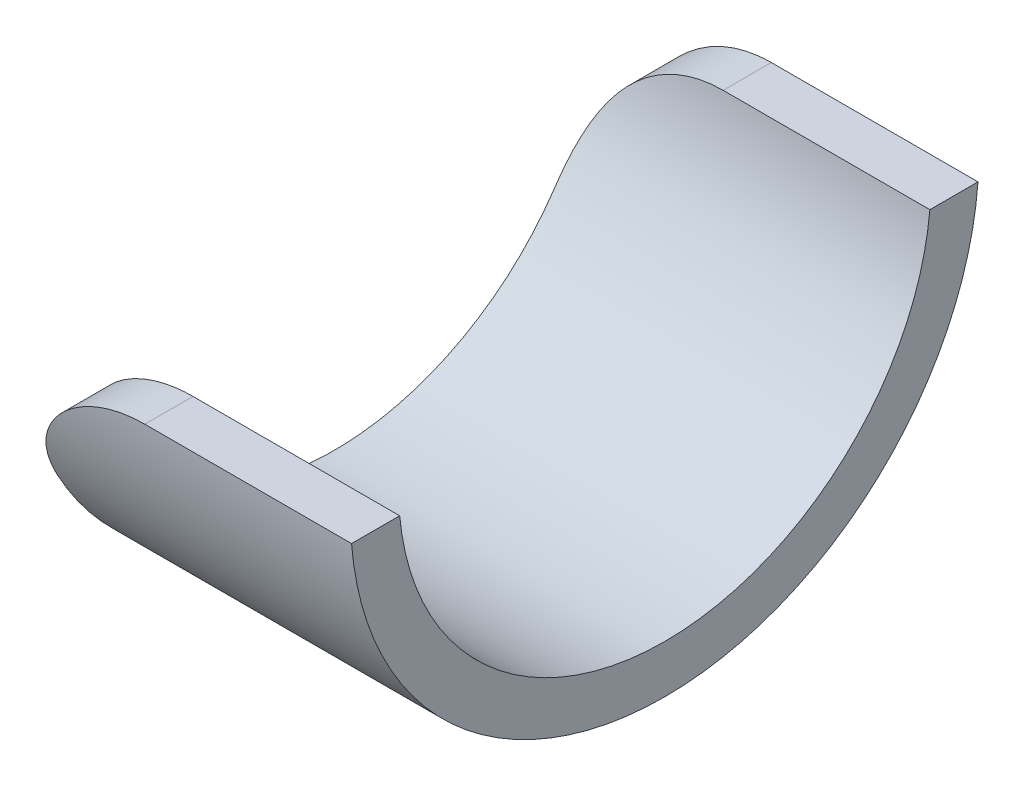
SolidWorks part; units mm, degrees
material "6061-T6 (SS)"
ref_plane "Front Plane" through (0, 0, 0) normal (0, 0, 1) x (1, 0, 0)
ref_plane "Top Plane" through (0, 0, 0) normal (0, 1, 0) x (1, 0, 0)
ref_plane "Right Plane" through (0, 0, 0) normal (1, 0, 0) x (0, 0, -1)
sketch "Sketch1" plane through (0, 0, 0) normal (1, 0, 0) x (0, 0, -1)
  line L0 (-24.0547, -1.905) -> (-20.3581, -1.905)
  line L1 (20.3581, -1.905) -> (24.0547, -1.905)
  arc A0 (-24.0547, -1.905) -> (24.0547, -1.905) centre (0, 0) ccw
  arc A1 (-20.3581, -1.905) -> (20.3581, -1.905) centre (0, 0) ccw
  point P1 (0, -24.13)
  dimension "D1" = 48.26
  dimension "D2" = 22.225
  dimension "D4" = 3.683
extrude "Boss-Extrude1" add sketch "Sketch1" along normal blind 25.4
fillet "Fillet1" radius 9.525 2 edges at (0, -1.905, -22.2064) (0, -1.905, 22.2064)
